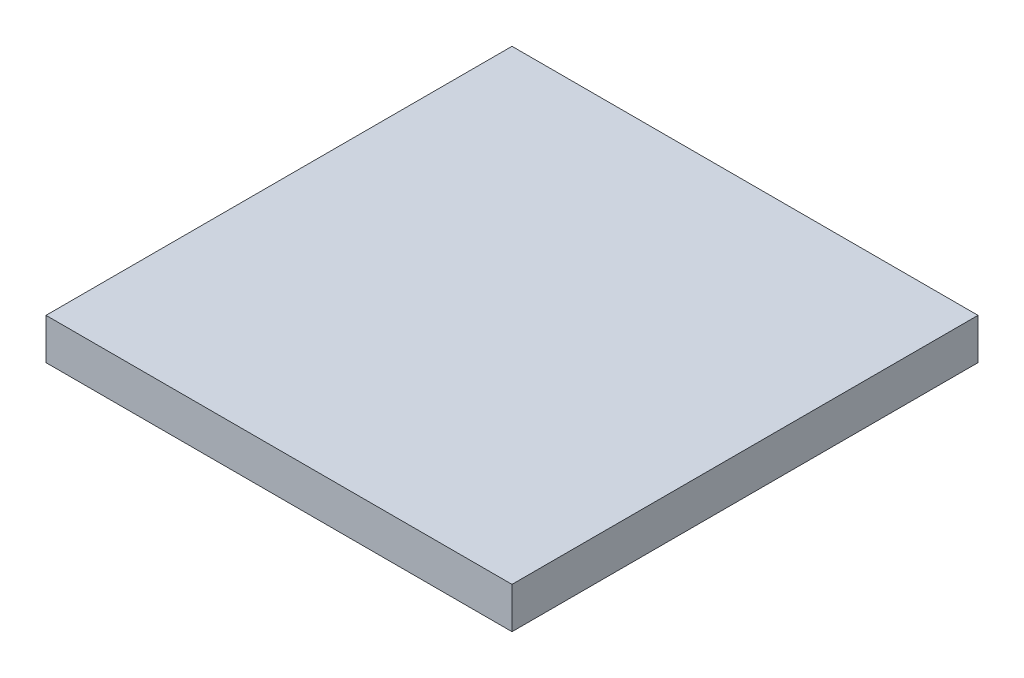
SolidWorks part; units mm, degrees
ref_plane "前视基准面" through (0, 0, 0) normal (0, 0, 1) x (1, 0, 0)
ref_plane "上视基准面" through (0, 0, 0) normal (0, 1, 0) x (1, 0, 0)
ref_plane "右视基准面" through (0, 0, 0) normal (1, 0, 0) x (0, 0, -1)
sketch "草图1" plane through (0, 0, 0) normal (0, 1, 0) x (1, 0, 0)
  line L1 (-6.25, 6.25) -> (6.25, 6.25)
  line L2 (-6.25, 6.25) -> (-6.25, -6.25)
  line L3 (-6.25, -6.25) -> (6.25, -6.25)
  line L4 (6.25, 6.25) -> (6.25, -6.25)
  line L5 (-6.25, 6.25) -> (6.25, -6.25) construction
  line L6 (-6.25, -6.25) -> (6.25, 6.25) construction
  point P0 (0, 0)
  dimension "D1" = 12.5
  dimension "D2" = 12.5
extrude "凸台-拉伸1" add sketch "草图1" along normal blind 1.1
